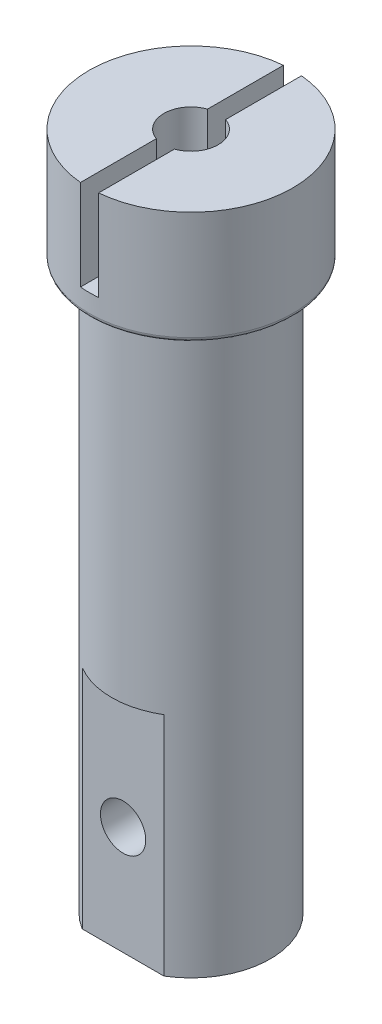
SolidWorks part; units mm, degrees
material "3003 Alloy"
ref_plane "Front Plane" through (0, 0, 0) normal (0, 0, 1) x (1, 0, 0)
ref_plane "Top Plane" through (0, 0, 0) normal (0, 1, 0) x (1, 0, 0)
ref_plane "Right Plane" through (0, 0, 0) normal (1, 0, 0) x (0, 0, -1)
sketch "StockDiameter" plane through (0, 0, 0) normal (0, 1, 0) x (1, 0, 0)
  circle A0 centre (0, 0) radius 22.5
  dimension "D1" = 45
extrude "BaseStock" add sketch "StockDiameter" against normal blind 150
sketch "Sketch11" plane through (0, 0, 0) normal (0, 1, 0) x (1, 0, 0)
  circle A0 centre (0, 0) radius 17.5
  dimension "D1" = 35
extrude "DiameterCut" cut sketch "Sketch11" against normal through all from offset 25 flip side to cut offset against normal yes
sketch "ShaftHole" plane through (0, 0, 0) normal (0, 1, 0) x (1, 0, 0)
  circle A0 centre (0, 0) radius 6
  dimension "D1" = 12
extrude "Motor1ShaftHole" cut sketch "ShaftHole" against normal through all
sketch "Sketch10" plane through (0, 0, 0) normal (0, 0, 1) x (1, 0, 0)
  line L0 (22.5, 0) -> (-22.5, 0) construction
  line L1 (2, 0) -> (-2, 0)
  line L2 (2, 0) -> (2, -20)
  line L3 (2, -20) -> (-2, -20)
  line L4 (-2, 0) -> (-2, -20)
  line L5 (2, 0) -> (-2, -20) construction
  line L6 (2, -20) -> (-2, 0) construction
  point P0 (0, -10)
  point P8 (0, 0)
  dimension "D1" = 4
  dimension "D2" = 20
extrude "ShaftKey" cut sketch "Sketch10" against normal through all both and the other way through all contours L4 L3 L2 L1
sketch "ArmKeySketch" plane through (0, 0, 0) normal (0, 1, 0) x (1, 0, 0)
  line L1 (-30, -35) -> (30, -35)
  line L2 (-30, -35) -> (-30, -15)
  line L3 (-30, -15) -> (30, -15)
  line L4 (30, -35) -> (30, -15)
  point P4 (0, -15)
  dimension "D1" = 15
  dimension "D2" = 20
  dimension "D3" = 60
extrude "ArmKey" cut sketch "ArmKeySketch" along normal blind 50 from surface at -150 starting at face at (0, -150, 6)
sketch "Sketch13" plane through (0, 0, 0) normal (0, 0, 1) x (1, 0, 0)
  line L0 (9.0139, -150) -> (-9.0139, -150) construction
  circle A0 centre (0, -126) radius 5
  dimension "D2" = 10
  dimension "D1" = 24
extrude "Arm1MountingHole" cut sketch "Sketch13" against normal up to surface (11.6834 mm away) from surface at 15 starting at face at (0, -125, 15)
fillet "Fillet1" radius 1 1 edges at (0, -25, 22.5)
equation "\"KeyDist\"= 15"
equation "\"D1@ArmKeySketch\"=\"KeyDist\""
equation "\"ArmWidth\"= 50"
equation "\"DrillHoleHeight\"= 24"
equation "\"D1@Sketch13\"=\"DrillHoleHeight\""
